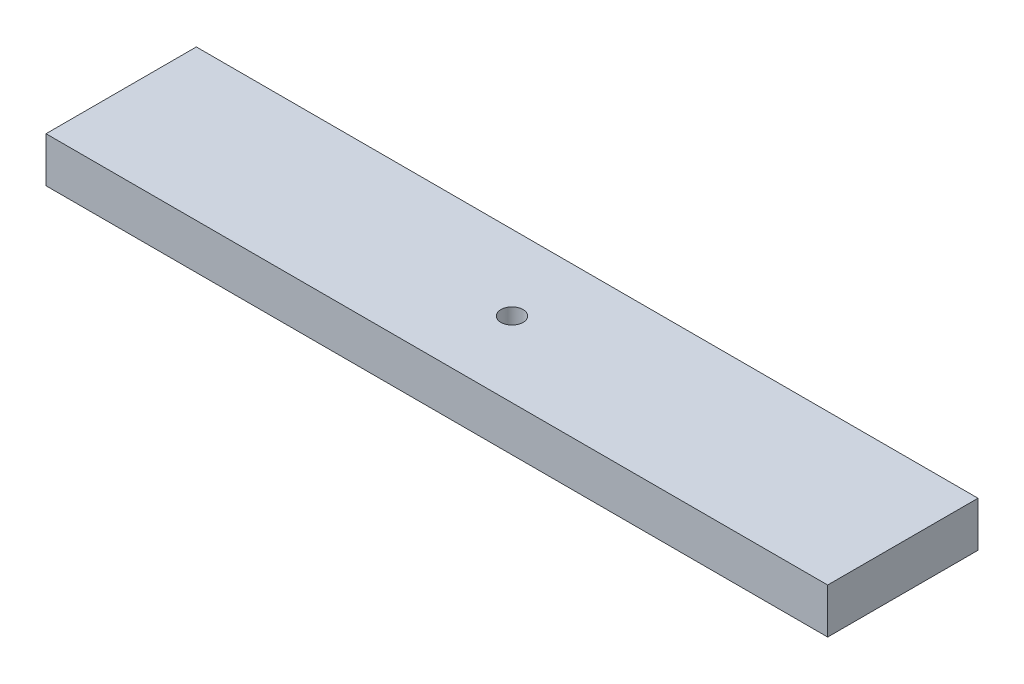
SolidWorks part; units mm, degrees
ref_plane "Front Plane" through (0, 0, 0) normal (0, 0, 1) x (1, 0, 0)
ref_plane "Top Plane" through (0, 0, 0) normal (0, 1, 0) x (1, 0, 0)
ref_plane "Right Plane" through (0, 0, 0) normal (1, 0, 0) x (0, 0, -1)
sketch "Sketch2" plane through (0, 0, 0) normal (0, 0, 1) x (1, 0, 0)
  line L0 (0, -9236.7196) -> (0, 452599.2593) construction
  line L1 (-9236.7196, 0) -> (452599.2593, 0) construction
  line L2 (-165.1, -976.8706) -> (-165.1, 49023.1294) construction
  line L3 (165.1, -978.9672) -> (165.1, 49021.0328) construction
  line L5 (-165.1, 0) -> (165.1, 0)
  line L6 (-165.1, 0) -> (-165.1, 19.05)
  line L7 (-165.1, 19.05) -> (165.1, 19.05)
  line L8 (165.1, 0) -> (165.1, 19.05)
  dimension "D1" = 165.1
  dimension "D2" = 165.1
  dimension "D3" = 19.05
  dimension "D4" = 330.2
extrude "Boss-Extrude1" add sketch "Sketch2" along normal blind 63.5
sketch "Sketch4" plane through (0, 0, 0) normal (0, 1, 0) x (1, 0, 0)
  line L0 (0, -1000) -> (0, 49000) construction
  circle A0 centre (0, -31.75) radius 4.699
  dimension "D1" = 31.75
  dimension "D2" = 9.398
extrude "Cut-Extrude2" cut sketch "Sketch4" along normal through all
